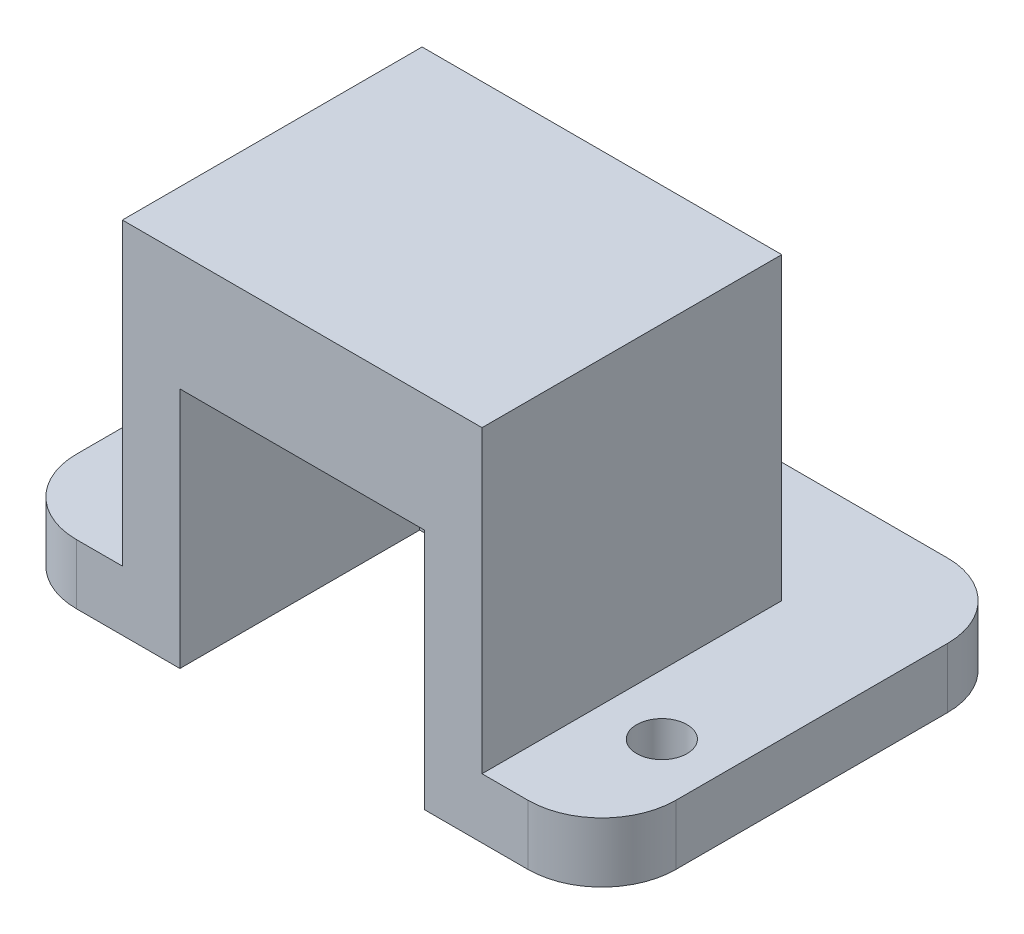
SolidWorks part; units mm, degrees
ref_plane "정면" through (0, 0, 0) normal (0, 0, 1) x (1, 0, 0)
ref_plane "윗면" through (0, 0, 0) normal (0, 1, 0) x (1, 0, 0)
ref_plane "우측면" through (0, 0, 0) normal (1, 0, 0) x (0, 0, -1)
sketch "스케치1" plane through (0, 0, 0) normal (0, 0, 1) x (1, 0, 0)
  line L1 (-15, 15) -> (15, 15)
  line L2 (-15, 15) -> (-15, -15)
  line L3 (-15, -15) -> (15, -15)
  line L4 (15, 15) -> (15, -15)
  line L5 (-15, 15) -> (15, -15) construction
  line L6 (-15, -15) -> (15, 15) construction
  point P4 (0, 0)
  point P5 (0, 0)
  point P6 (0, 0)
  dimension "D1" = 30
  dimension "D2" = 30
extrude "보스-돌출1" add sketch "스케치1" along normal blind 5 contours L1 L4 L3 L2
sketch "스케치2" plane through (0, 0, 0) normal (0, 0, -1) x (-1, 0, 0)
  line L0 (15, 15) -> (15, -15) construction
  line L1 (-15, -15) -> (15, -15)
  line L2 (-15, -15) -> (-15, -10)
  line L3 (-15, -10) -> (15, -10)
  line L4 (15, -15) -> (15, -10)
  line L5 (-15, -15) -> (15, -10) construction
  line L6 (-15, -10) -> (15, -15) construction
  point P4 (0, -12.5)
  dimension "D1" = 5
extrude "보스-돌출2" add sketch "스케치2" along normal blind 10
sketch "스케치3" plane through (0, -10, 0) normal (0, 1, 0) x (1, 0, 0)
  line L0 (-15, 10) -> (15, 10) construction
  circle A0 centre (0, 5) radius 2.1
  point P4 (0, 0)
  point P5 (0, 0)
  point P6 (0, 10)
  dimension "D1" = 4.2
  dimension "D2" = 5
extrude "컷-돌출1" cut sketch "스케치3" against normal blind 5
sketch "스케치4" plane through (0, 0, 5) normal (0, 0, 1) x (1, 0, 0)
  line L0 (10.2, -15) -> (15, -15)
  line L1 (-15, -15) -> (-10.2, -15)
  line L2 (-15, -15) -> (-15, 15)
  line L3 (-15, 15) -> (15, 15)
  line L4 (15, -15) -> (15, 15)
  line L5 (-15, -15) -> (15, 15) construction
  line L6 (-15, 15) -> (15, -15) construction
  line L8 (-10.2, -15) -> (-10.2, 5.2)
  line L9 (-10.2, 5.2) -> (10.2, 5.2)
  line L10 (10.2, -15) -> (10.2, 5.2)
  line L11 (-10.2, -15) -> (10.2, 5.2) construction
  line L12 (-10.2, 5.2) -> (10.2, -15) construction
  point P4 (0, 0)
  point P11 (0, -4.9)
  dimension "D1" = 4.8
  dimension "D2" = 4.8
  dimension "D3" = 9.8
extrude "보스-돌출3" add sketch "스케치4" along normal blind 20
sketch "스케치5" plane through (-15, 0, 0) normal (-1, 0, 0) x (0, 0, 1)
  line L0 (25, 15) -> (25, -15) construction
  line L1 (-10, -15) -> (25, -15)
  line L2 (-10, -15) -> (-10, -10)
  line L3 (-10, -10) -> (25, -10)
  line L4 (25, -15) -> (25, -10)
  line L5 (-10, -15) -> (25, -10) construction
  line L6 (-10, -10) -> (25, -15) construction
  point P4 (7.5, -12.5)
  dimension "D1" = 5
extrude "보스-돌출4" add sketch "스케치5" along normal blind 10
sketch "스케치6" plane through (15, 0, 0) normal (1, 0, 0) x (0, 0, -1)
  line L1 (-25, -15) -> (10, -15)
  line L2 (-25, -15) -> (-25, -10)
  line L3 (-25, -10) -> (10, -10)
  line L4 (10, -15) -> (10, -10)
  line L5 (-25, -15) -> (10, -10) construction
  line L6 (-25, -10) -> (10, -15) construction
  point P4 (-7.5, -12.5)
extrude "보스-돌출5" add sketch "스케치6" along normal blind 10
sketch "스케치7" plane through (0, -10, 0) normal (0, 1, 0) x (1, 0, 0)
  line L0 (-25, -25) -> (-25, 10) construction
  line L1 (25, 10) -> (25, -25) construction
  line L2 (-25, -25) -> (-15, -25) construction
  circle A0 centre (-20, -15) radius 2.1
  circle A1 centre (20, -15) radius 2.1
  point P8 (0, 0)
  dimension "D1" = 4.2
  dimension "D2" = 5
  dimension "D3" = 5
  dimension "D4" = 10
extrude "컷-돌출2" cut sketch "스케치7" against normal blind 10
fillet "필렛1" radius 6.17 1 edges at (25, -12.5, 25)
fillet "필렛2" radius 6.17 1 edges at (25, -12.5, -10)
fillet "필렛3" radius 6.17 1 edges at (-25, -12.5, 25)
fillet "필렛4" radius 6.17 1 edges at (-25, -12.5, -10)
